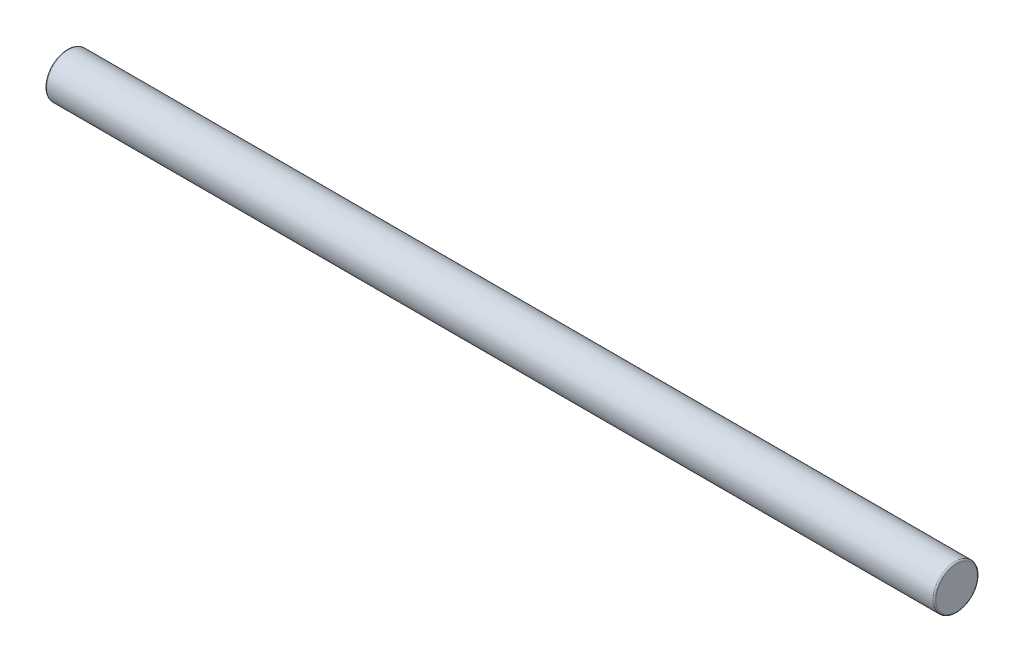
SolidWorks part; units mm, degrees
ref_plane "Front Plane" through (0, 0, 0) normal (0, 0, 1) x (1, 0, 0)
ref_plane "Top Plane" through (0, 0, 0) normal (0, 1, 0) x (1, 0, 0)
ref_plane "Right Plane" through (0, 0, 0) normal (1, 0, 0) x (0, 0, -1)
sketch "Sketch1" plane through (0, 0, 0) normal (1, 0, 0) x (0, 0, -1)
  circle A0 centre (0, 0) radius 0.381
  dimension "D1" = 0.762
extrude "Extrude1" add sketch "Sketch1" along normal blind 15.24
fillet "Fillet1" radius 0.0254 2 edges at (0, 0, -0.381) (15.24, 0, -0.381)
